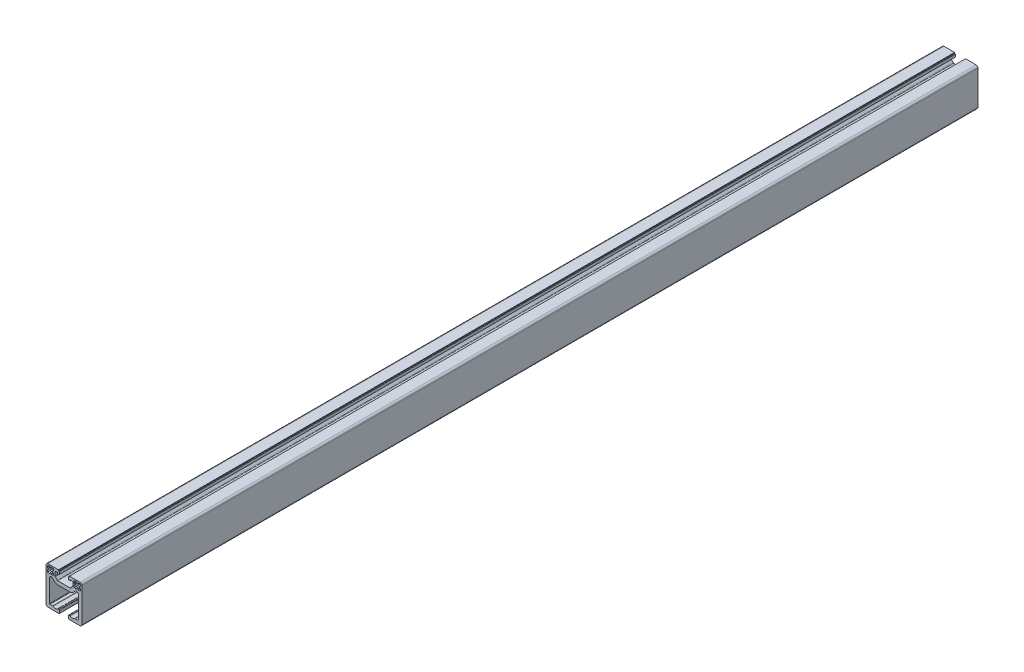
SolidWorks part; units mm, degrees
ref_plane "前视基准面" through (0, 0, 0) normal (0, 0, 1) x (1, 0, 0)
ref_plane "上视基准面" through (0, 0, 0) normal (0, 1, 0) x (1, 0, 0)
ref_plane "右视基准面" through (0, 0, 0) normal (1, 0, 0) x (0, 0, -1)
sketch "Model" plane through (0, 0, 0) normal (0, 0, 1) x (1, 0, 0)
  line L0 (1653.8679, 609.9355) -> (1656.8679, 609.9355)
  line L1 (1662.8679, 609.9355) -> (1663.8679, 609.9355)
  line L2 (1664.3679, 609.4355) -> (1664.3679, 606.4355)
  line L3 (1663.8679, 605.9355) -> (1651.3679, 605.9355)
  line L4 (1649.3679, 607.9355) -> (1649.3679, 645.9355)
  line L5 (1651.3679, 647.9355) -> (1663.2679, 647.9355)
  line L6 (1663.2679, 647.9355) -> (1663.2679, 646.9355)
  line L7 (1663.2679, 646.9355) -> (1664.2679, 646.9355)
  line L8 (1664.2679, 646.9355) -> (1664.2679, 643.9355)
  line L9 (1664.2679, 643.9355) -> (1662.2679, 643.9355)
  line L10 (1662.2679, 643.9355) -> (1662.2679, 644.9355)
  line L11 (1662.2679, 644.9355) -> (1660.3679, 644.9355)
  line L12 (1659.3679, 643.9355) -> (1659.3679, 640.1175)
  line L13 (1659.6608, 639.4104) -> (1661.8428, 637.2284)
  line L14 (1662.5499, 636.9355) -> (1676.186, 636.9355)
  line L15 (1676.8931, 637.2284) -> (1679.0751, 639.4104)
  line L16 (1679.3679, 640.1175) -> (1679.3679, 643.9355)
  line L17 (1678.3679, 644.9355) -> (1676.4679, 644.9355)
  line L18 (1676.4679, 644.9355) -> (1676.4679, 643.9355)
  line L19 (1676.4679, 643.9355) -> (1674.4679, 643.9355)
  line L20 (1674.4679, 643.9355) -> (1674.4679, 646.9355)
  line L21 (1674.4679, 646.9355) -> (1675.4679, 646.9355)
  line L22 (1675.4679, 646.9355) -> (1675.4679, 647.9355)
  line L23 (1675.4679, 647.9355) -> (1687.3679, 647.9355)
  line L24 (1689.3679, 645.9355) -> (1689.3679, 607.9355)
  line L25 (1687.3679, 605.9355) -> (1674.8679, 605.9355)
  line L26 (1674.3679, 606.4355) -> (1674.3679, 609.4355)
  line L27 (1674.8679, 609.9355) -> (1675.8679, 609.9355)
  line L28 (1681.8679, 609.9355) -> (1684.8679, 609.9355)
  line L29 (1685.3679, 610.4355) -> (1685.3679, 635.218)
  line L30 (1681.9537, 636.6322) -> (1679.7215, 634.4)
  line L31 (1676.186, 632.9355) -> (1662.5499, 632.9355)
  line L32 (1659.0144, 634.4) -> (1656.7822, 636.6322)
  line L33 (1653.3679, 635.218) -> (1653.3679, 610.4355)
  line L34 (1657.8679, 639.4355) -> (1655.1679, 639.4355)
  line L35 (1686.8679, 643.7355) -> (1687.8679, 643.7355)
  line L36 (1687.8679, 643.7355) -> (1687.8679, 645.4355)
  line L37 (1686.8679, 642.1355) -> (1686.8679, 643.7355)
  line L38 (1687.8679, 642.1355) -> (1686.8679, 642.1355)
  line L39 (1686.8679, 646.4355) -> (1685.1679, 646.4355)
  line L40 (1687.8679, 639.4355) -> (1687.8679, 642.1355)
  line L41 (1685.1679, 646.4355) -> (1685.1679, 645.4355)
  line L42 (1685.1679, 639.4355) -> (1687.8679, 639.4355)
  line L43 (1685.1679, 645.4355) -> (1683.5679, 645.4355)
  line L44 (1685.1679, 640.4355) -> (1685.1679, 639.4355)
  line L45 (1683.5679, 645.4355) -> (1683.5679, 646.4355)
  line L46 (1683.5679, 640.4355) -> (1685.1679, 640.4355)
  line L47 (1683.5679, 646.4355) -> (1680.8679, 646.4355)
  line L48 (1683.5679, 639.4355) -> (1683.5679, 640.4355)
  line L49 (1680.8679, 646.4355) -> (1680.8679, 643.7355)
  line L50 (1680.8679, 639.4355) -> (1683.5679, 639.4355)
  line L51 (1680.8679, 643.7355) -> (1681.8679, 643.7355)
  line L52 (1680.8679, 642.1355) -> (1680.8679, 639.4355)
  line L53 (1681.8679, 643.7355) -> (1681.8679, 642.1355)
  line L54 (1681.8679, 642.1355) -> (1680.8679, 642.1355)
  line L55 (1656.8679, 643.7355) -> (1657.8679, 643.7355)
  line L56 (1657.8679, 643.7355) -> (1657.8679, 646.4355)
  line L57 (1656.8679, 642.1355) -> (1656.8679, 643.7355)
  line L58 (1657.8679, 646.4355) -> (1655.1679, 646.4355)
  line L59 (1657.8679, 642.1355) -> (1656.8679, 642.1355)
  line L60 (1655.1679, 646.4355) -> (1655.1679, 645.4355)
  line L61 (1657.8679, 639.4355) -> (1657.8679, 642.1355)
  line L62 (1655.1679, 645.4355) -> (1653.5679, 645.4355)
  line L63 (1655.1679, 639.4355) -> (1657.8679, 639.4355)
  line L64 (1653.5679, 645.4355) -> (1653.5679, 646.4355)
  line L65 (1655.1679, 640.4355) -> (1655.1679, 639.4355)
  line L66 (1653.5679, 646.4355) -> (1651.8679, 646.4355)
  line L67 (1653.5679, 640.4355) -> (1655.1679, 640.4355)
  line L68 (1653.5679, 639.4355) -> (1653.5679, 640.4355)
  line L69 (1650.8679, 645.4355) -> (1650.8679, 643.7355)
  line L70 (1650.8679, 639.4355) -> (1653.5679, 639.4355)
  line L71 (1650.8679, 643.7355) -> (1651.8679, 643.7355)
  line L72 (1650.8679, 642.1355) -> (1650.8679, 639.4355)
  line L73 (1651.8679, 643.7355) -> (1651.8679, 642.1355)
  line L74 (1651.8679, 642.1355) -> (1650.8679, 642.1355)
  line L75 (1657.8679, 639.4355) -> (1655.1679, 639.4355)
  line L76 (1655.1679, 639.4355) -> (1655.1679, 640.4355)
  line L77 (1655.1679, 640.4355) -> (1653.5679, 640.4355)
  line L78 (1653.5679, 640.4355) -> (1653.5679, 639.4355)
  line L79 (1653.5679, 639.4355) -> (1650.8679, 639.4355)
  line L80 (1650.8679, 639.4355) -> (1650.8679, 642.1355)
  line L81 (1650.8679, 642.1355) -> (1651.8679, 642.1355)
  line L82 (1651.8679, 642.1355) -> (1651.8679, 643.7355)
  line L83 (1651.8679, 643.7355) -> (1650.8679, 643.7355)
  line L84 (1650.8679, 643.7355) -> (1650.8679, 645.4355)
  line L85 (1651.8679, 646.4355) -> (1653.5679, 646.4355)
  line L86 (1653.5679, 646.4355) -> (1653.5679, 645.4355)
  line L87 (1653.5679, 645.4355) -> (1655.1679, 645.4355)
  line L88 (1655.1679, 645.4355) -> (1655.1679, 646.4355)
  line L89 (1655.1679, 646.4355) -> (1657.8679, 646.4355)
  line L90 (1657.8679, 646.4355) -> (1657.8679, 643.7355)
  line L91 (1657.8679, 643.7355) -> (1656.8679, 643.7355)
  line L92 (1656.8679, 643.7355) -> (1656.8679, 642.1355)
  line L93 (1656.8679, 642.1355) -> (1657.8679, 642.1355)
  line L94 (1657.8679, 642.1355) -> (1657.8679, 639.4355)
  line L95 (1680.8679, 639.4355) -> (1680.8679, 642.1355)
  line L96 (1680.8679, 642.1355) -> (1681.8679, 642.1355)
  line L97 (1681.8679, 642.1355) -> (1681.8679, 643.7355)
  line L98 (1681.8679, 643.7355) -> (1680.8679, 643.7355)
  line L99 (1680.8679, 643.7355) -> (1680.8679, 646.4355)
  line L100 (1680.8679, 646.4355) -> (1683.5679, 646.4355)
  line L101 (1683.5679, 646.4355) -> (1683.5679, 645.4355)
  line L102 (1683.5679, 645.4355) -> (1685.1679, 645.4355)
  line L103 (1685.1679, 645.4355) -> (1685.1679, 646.4355)
  line L104 (1685.1679, 646.4355) -> (1686.8679, 646.4355)
  line L105 (1687.8679, 645.4355) -> (1687.8679, 643.7355)
  line L106 (1687.8679, 643.7355) -> (1686.8679, 643.7355)
  line L107 (1686.8679, 643.7355) -> (1686.8679, 642.1355)
  line L108 (1686.8679, 642.1355) -> (1687.8679, 642.1355)
  line L109 (1687.8679, 642.1355) -> (1687.8679, 639.4355)
  line L110 (1687.8679, 639.4355) -> (1685.1679, 639.4355)
  line L111 (1685.1679, 639.4355) -> (1685.1679, 640.4355)
  line L112 (1685.1679, 640.4355) -> (1683.5679, 640.4355)
  line L113 (1683.5679, 640.4355) -> (1683.5679, 639.4355)
  line L114 (1683.5679, 639.4355) -> (1680.8679, 639.4355)
  line L115 (1687.3679, 647.9355) -> (1675.4679, 647.9355)
  line L116 (1675.4679, 647.9355) -> (1675.4679, 646.9355)
  line L117 (1675.4679, 646.9355) -> (1674.4679, 646.9355)
  line L118 (1674.4679, 646.9355) -> (1674.4679, 643.9355)
  line L119 (1674.4679, 643.9355) -> (1676.4679, 643.9355)
  line L120 (1676.4679, 643.9355) -> (1676.4679, 644.9355)
  line L121 (1676.4679, 644.9355) -> (1678.3679, 644.9355)
  line L122 (1679.3679, 643.9355) -> (1679.3679, 640.1175)
  line L123 (1679.0751, 639.4104) -> (1676.8931, 637.2284)
  line L124 (1676.186, 636.9355) -> (1662.5499, 636.9355)
  line L125 (1661.8428, 637.2284) -> (1659.6608, 639.4104)
  line L126 (1659.3679, 640.1175) -> (1659.3679, 643.9355)
  line L127 (1660.3679, 644.9355) -> (1662.2679, 644.9355)
  line L128 (1662.2679, 644.9355) -> (1662.2679, 643.9355)
  line L129 (1662.2679, 643.9355) -> (1664.2679, 643.9355)
  line L130 (1664.2679, 643.9355) -> (1664.2679, 646.9355)
  line L131 (1664.2679, 646.9355) -> (1663.2679, 646.9355)
  line L132 (1663.2679, 646.9355) -> (1663.2679, 647.9355)
  line L133 (1663.2679, 647.9355) -> (1651.3679, 647.9355)
  line L134 (1649.3679, 645.9355) -> (1649.3679, 607.9355)
  line L135 (1651.3679, 605.9355) -> (1663.8679, 605.9355)
  line L136 (1664.3679, 606.4355) -> (1664.3679, 609.4355)
  line L137 (1663.8679, 609.9355) -> (1662.8679, 609.9355)
  line L138 (1656.8679, 609.9355) -> (1653.8679, 609.9355)
  line L139 (1653.3679, 610.4355) -> (1653.3679, 635.218)
  line L140 (1656.7822, 636.6322) -> (1659.0144, 634.4)
  line L141 (1662.5499, 632.9355) -> (1676.186, 632.9355)
  line L142 (1679.7215, 634.4) -> (1681.9537, 636.6322)
  line L143 (1685.3679, 635.218) -> (1685.3679, 610.4355)
  line L144 (1684.8679, 609.9355) -> (1681.8679, 609.9355)
  line L145 (1675.8679, 609.9355) -> (1674.8679, 609.9355)
  line L146 (1674.3679, 609.4355) -> (1674.3679, 606.4355)
  line L147 (1674.8679, 605.9355) -> (1687.3679, 605.9355)
  line L148 (1689.3679, 607.9355) -> (1689.3679, 645.9355)
  line L149 (1655.1679, 639.4355) -> (1655.1679, 640.4355)
  line L150 (1655.1679, 640.4355) -> (1653.5679, 640.4355)
  line L151 (1653.5679, 640.4355) -> (1653.5679, 639.4355)
  line L152 (1653.5679, 639.4355) -> (1650.8679, 639.4355)
  line L153 (1650.8679, 639.4355) -> (1650.8679, 642.1355)
  line L154 (1650.8679, 642.1355) -> (1651.8679, 642.1355)
  line L155 (1651.8679, 642.1355) -> (1651.8679, 643.7355)
  line L156 (1651.8679, 643.7355) -> (1650.8679, 643.7355)
  line L157 (1650.8679, 643.7355) -> (1650.8679, 645.4355)
  line L158 (1651.8679, 646.4355) -> (1653.5679, 646.4355)
  line L159 (1653.5679, 646.4355) -> (1653.5679, 645.4355)
  line L160 (1653.5679, 645.4355) -> (1655.1679, 645.4355)
  line L161 (1655.1679, 645.4355) -> (1655.1679, 646.4355)
  line L162 (1655.1679, 646.4355) -> (1657.8679, 646.4355)
  line L163 (1657.8679, 646.4355) -> (1657.8679, 643.7355)
  line L164 (1657.8679, 643.7355) -> (1656.8679, 643.7355)
  line L165 (1656.8679, 643.7355) -> (1656.8679, 642.1355)
  line L166 (1656.8679, 642.1355) -> (1657.8679, 642.1355)
  line L167 (1657.8679, 642.1355) -> (1657.8679, 639.4355)
  line L168 (1657.8679, 639.4355) -> (1655.1679, 639.4355)
  line L169 (1680.8679, 642.1355) -> (1681.8679, 642.1355)
  line L170 (1681.8679, 642.1355) -> (1681.8679, 643.7355)
  line L171 (1681.8679, 643.7355) -> (1680.8679, 643.7355)
  line L172 (1680.8679, 643.7355) -> (1680.8679, 646.4355)
  line L173 (1680.8679, 646.4355) -> (1683.5679, 646.4355)
  line L174 (1683.5679, 646.4355) -> (1683.5679, 645.4355)
  line L175 (1683.5679, 645.4355) -> (1685.1679, 645.4355)
  line L176 (1685.1679, 645.4355) -> (1685.1679, 646.4355)
  line L177 (1685.1679, 646.4355) -> (1686.8679, 646.4355)
  line L178 (1687.8679, 645.4355) -> (1687.8679, 643.7355)
  line L179 (1687.8679, 643.7355) -> (1686.8679, 643.7355)
  line L180 (1686.8679, 643.7355) -> (1686.8679, 642.1355)
  line L181 (1686.8679, 642.1355) -> (1687.8679, 642.1355)
  line L182 (1687.8679, 642.1355) -> (1687.8679, 639.4355)
  line L183 (1687.8679, 639.4355) -> (1685.1679, 639.4355)
  line L184 (1685.1679, 639.4355) -> (1685.1679, 640.4355)
  line L185 (1685.1679, 640.4355) -> (1683.5679, 640.4355)
  line L186 (1683.5679, 640.4355) -> (1683.5679, 639.4355)
  line L187 (1683.5679, 639.4355) -> (1680.8679, 639.4355)
  line L188 (1680.8679, 639.4355) -> (1680.8679, 642.1355)
  line L189 (1679.7215, 634.4) -> (1681.9537, 636.6322)
  line L190 (1685.3679, 635.218) -> (1685.3679, 610.4355)
  line L191 (1684.8679, 609.9355) -> (1681.8679, 609.9355)
  line L192 (1675.8679, 609.9355) -> (1674.8679, 609.9355)
  line L193 (1674.3679, 609.4355) -> (1674.3679, 606.4355)
  line L194 (1674.8679, 605.9355) -> (1687.3679, 605.9355)
  line L195 (1689.3679, 607.9355) -> (1689.3679, 645.9355)
  line L196 (1687.3679, 647.9355) -> (1675.4679, 647.9355)
  line L197 (1675.4679, 647.9355) -> (1675.4679, 646.9355)
  line L198 (1675.4679, 646.9355) -> (1674.4679, 646.9355)
  line L199 (1674.4679, 646.9355) -> (1674.4679, 643.9355)
  line L200 (1674.4679, 643.9355) -> (1676.4679, 643.9355)
  line L201 (1676.4679, 643.9355) -> (1676.4679, 644.9355)
  line L202 (1676.4679, 644.9355) -> (1678.3679, 644.9355)
  line L203 (1679.3679, 643.9355) -> (1679.3679, 640.1175)
  line L204 (1679.0751, 639.4104) -> (1676.8931, 637.2284)
  line L205 (1676.186, 636.9355) -> (1662.5499, 636.9355)
  line L206 (1661.8428, 637.2284) -> (1659.6608, 639.4104)
  line L207 (1659.3679, 640.1175) -> (1659.3679, 643.9355)
  line L208 (1660.3679, 644.9355) -> (1662.2679, 644.9355)
  line L209 (1662.2679, 644.9355) -> (1662.2679, 643.9355)
  line L210 (1662.2679, 643.9355) -> (1664.2679, 643.9355)
  line L211 (1664.2679, 643.9355) -> (1664.2679, 646.9355)
  line L212 (1664.2679, 646.9355) -> (1663.2679, 646.9355)
  line L213 (1663.2679, 646.9355) -> (1663.2679, 647.9355)
  line L214 (1663.2679, 647.9355) -> (1651.3679, 647.9355)
  line L215 (1649.3679, 645.9355) -> (1649.3679, 607.9355)
  line L216 (1651.3679, 605.9355) -> (1663.8679, 605.9355)
  line L217 (1664.3679, 606.4355) -> (1664.3679, 609.4355)
  line L218 (1663.8679, 609.9355) -> (1662.8679, 609.9355)
  line L219 (1656.8679, 609.9355) -> (1653.8679, 609.9355)
  line L220 (1653.3679, 610.4355) -> (1653.3679, 635.218)
  line L221 (1656.7822, 636.6322) -> (1659.0144, 634.4)
  line L222 (1662.5499, 632.9355) -> (1676.186, 632.9355)
  arc A0 (1657.1679, 609.8355) -> (1656.8679, 609.9355) centre (1656.8679, 609.4355) ccw
  arc A1 (1657.1679, 609.8355) -> (1662.5679, 609.8355) centre (1659.8679, 613.4355) ccw
  arc A2 (1662.8679, 609.9355) -> (1662.5679, 609.8355) centre (1662.8679, 609.4355) ccw
  arc A3 (1664.3679, 609.4355) -> (1663.8679, 609.9355) centre (1663.8679, 609.4355) ccw
  arc A4 (1663.8679, 605.9355) -> (1664.3679, 606.4355) centre (1663.8679, 606.4355) ccw
  arc A5 (1649.3679, 607.9355) -> (1651.3679, 605.9355) centre (1651.3679, 607.9355) ccw
  arc A6 (1651.3679, 647.9355) -> (1649.3679, 645.9355) centre (1651.3679, 645.9355) ccw
  arc A7 (1660.3679, 644.9355) -> (1659.3679, 643.9355) centre (1660.3679, 643.9355) ccw
  arc A8 (1659.3679, 640.1175) -> (1659.6608, 639.4104) centre (1660.3679, 640.1175) ccw
  arc A9 (1661.8428, 637.2284) -> (1662.5499, 636.9355) centre (1662.5499, 637.9355) ccw
  arc A10 (1676.186, 636.9355) -> (1676.8931, 637.2284) centre (1676.186, 637.9355) ccw
  arc A11 (1679.0751, 639.4104) -> (1679.3679, 640.1175) centre (1678.3679, 640.1175) ccw
  arc A12 (1679.3679, 643.9355) -> (1678.3679, 644.9355) centre (1678.3679, 643.9355) ccw
  arc A13 (1689.3679, 645.9355) -> (1687.3679, 647.9355) centre (1687.3679, 645.9355) ccw
  arc A14 (1687.3679, 605.9355) -> (1689.3679, 607.9355) centre (1687.3679, 607.9355) ccw
  arc A15 (1674.3679, 606.4355) -> (1674.8679, 605.9355) centre (1674.8679, 606.4355) ccw
  arc A16 (1674.8679, 609.9355) -> (1674.3679, 609.4355) centre (1674.8679, 609.4355) ccw
  arc A17 (1676.1679, 609.8355) -> (1675.8679, 609.9355) centre (1675.8679, 609.4355) ccw
  arc A18 (1676.1679, 609.8355) -> (1681.5679, 609.8355) centre (1678.8679, 613.4355) ccw
  arc A19 (1681.8679, 609.9355) -> (1681.5679, 609.8355) centre (1681.8679, 609.4355) ccw
  arc A20 (1684.8679, 609.9355) -> (1685.3679, 610.4355) centre (1684.8679, 610.4355) ccw
  arc A21 (1685.3679, 635.218) -> (1681.9537, 636.6322) centre (1683.3679, 635.218) ccw
  arc A22 (1676.186, 632.9355) -> (1679.7215, 634.4) centre (1676.186, 637.9355) ccw
  arc A23 (1659.0144, 634.4) -> (1662.5499, 632.9355) centre (1662.5499, 637.9355) ccw
  arc A24 (1656.7822, 636.6322) -> (1653.3679, 635.218) centre (1655.3679, 635.218) ccw
  arc A25 (1653.3679, 610.4355) -> (1653.8679, 609.9355) centre (1653.8679, 610.4355) ccw
  arc A26 (1687.8679, 645.4355) -> (1686.8679, 646.4355) centre (1686.8679, 645.4355) ccw
  arc A27 (1651.8679, 646.4355) -> (1650.8679, 645.4355) centre (1651.8679, 645.4355) ccw
  arc A28 (1651.8679, 646.4355) -> (1650.8679, 645.4355) centre (1651.8679, 645.4355) ccw
  arc A29 (1687.8679, 645.4355) -> (1686.8679, 646.4355) centre (1686.8679, 645.4355) ccw
  arc A30 (1689.3679, 645.9355) -> (1687.3679, 647.9355) centre (1687.3679, 645.9355) ccw
  arc A31 (1679.3679, 643.9355) -> (1678.3679, 644.9355) centre (1678.3679, 643.9355) ccw
  arc A32 (1679.0751, 639.4104) -> (1679.3679, 640.1175) centre (1678.3679, 640.1175) ccw
  arc A33 (1676.186, 636.9355) -> (1676.8931, 637.2284) centre (1676.186, 637.9355) ccw
  arc A34 (1661.8428, 637.2284) -> (1662.5499, 636.9355) centre (1662.5499, 637.9355) ccw
  arc A35 (1659.3679, 640.1175) -> (1659.6608, 639.4104) centre (1660.3679, 640.1175) ccw
  arc A36 (1660.3679, 644.9355) -> (1659.3679, 643.9355) centre (1660.3679, 643.9355) ccw
  arc A37 (1651.3679, 647.9355) -> (1649.3679, 645.9355) centre (1651.3679, 645.9355) ccw
  arc A38 (1649.3679, 607.9355) -> (1651.3679, 605.9355) centre (1651.3679, 607.9355) ccw
  arc A39 (1663.8679, 605.9355) -> (1664.3679, 606.4355) centre (1663.8679, 606.4355) ccw
  arc A40 (1664.3679, 609.4355) -> (1663.8679, 609.9355) centre (1663.8679, 609.4355) ccw
  arc A41 (1662.8679, 609.9355) -> (1662.5679, 609.8355) centre (1662.8679, 609.4355) ccw
  arc A42 (1657.1679, 609.8355) -> (1662.5679, 609.8355) centre (1659.8679, 613.4355) ccw
  arc A43 (1657.1679, 609.8355) -> (1656.8679, 609.9355) centre (1656.8679, 609.4355) ccw
  arc A44 (1653.3679, 610.4355) -> (1653.8679, 609.9355) centre (1653.8679, 610.4355) ccw
  arc A45 (1656.7822, 636.6322) -> (1653.3679, 635.218) centre (1655.3679, 635.218) ccw
  arc A46 (1659.0144, 634.4) -> (1662.5499, 632.9355) centre (1662.5499, 637.9355) ccw
  arc A47 (1676.186, 632.9355) -> (1679.7215, 634.4) centre (1676.186, 637.9355) ccw
  arc A48 (1685.3679, 635.218) -> (1681.9537, 636.6322) centre (1683.3679, 635.218) ccw
  arc A49 (1684.8679, 609.9355) -> (1685.3679, 610.4355) centre (1684.8679, 610.4355) ccw
  arc A50 (1681.8679, 609.9355) -> (1681.5679, 609.8355) centre (1681.8679, 609.4355) ccw
  arc A51 (1676.1679, 609.8355) -> (1681.5679, 609.8355) centre (1678.8679, 613.4355) ccw
  arc A52 (1676.1679, 609.8355) -> (1675.8679, 609.9355) centre (1675.8679, 609.4355) ccw
  arc A53 (1674.8679, 609.9355) -> (1674.3679, 609.4355) centre (1674.8679, 609.4355) ccw
  arc A54 (1674.3679, 606.4355) -> (1674.8679, 605.9355) centre (1674.8679, 606.4355) ccw
  arc A55 (1687.3679, 605.9355) -> (1689.3679, 607.9355) centre (1687.3679, 607.9355) ccw
  arc A56 (1651.8679, 646.4355) -> (1650.8679, 645.4355) centre (1651.8679, 645.4355) ccw
  arc A57 (1687.8679, 645.4355) -> (1686.8679, 646.4355) centre (1686.8679, 645.4355) ccw
  arc A58 (1685.3679, 635.218) -> (1681.9537, 636.6322) centre (1683.3679, 635.218) ccw
  arc A59 (1684.8679, 609.9355) -> (1685.3679, 610.4355) centre (1684.8679, 610.4355) ccw
  arc A60 (1681.8679, 609.9355) -> (1681.5679, 609.8355) centre (1681.8679, 609.4355) ccw
  arc A61 (1676.1679, 609.8355) -> (1681.5679, 609.8355) centre (1678.8679, 613.4355) ccw
  arc A62 (1676.1679, 609.8355) -> (1675.8679, 609.9355) centre (1675.8679, 609.4355) ccw
  arc A63 (1674.8679, 609.9355) -> (1674.3679, 609.4355) centre (1674.8679, 609.4355) ccw
  arc A64 (1674.3679, 606.4355) -> (1674.8679, 605.9355) centre (1674.8679, 606.4355) ccw
  arc A65 (1687.3679, 605.9355) -> (1689.3679, 607.9355) centre (1687.3679, 607.9355) ccw
  arc A66 (1689.3679, 645.9355) -> (1687.3679, 647.9355) centre (1687.3679, 645.9355) ccw
  arc A67 (1679.3679, 643.9355) -> (1678.3679, 644.9355) centre (1678.3679, 643.9355) ccw
  arc A68 (1679.0751, 639.4104) -> (1679.3679, 640.1175) centre (1678.3679, 640.1175) ccw
  arc A69 (1676.186, 636.9355) -> (1676.8931, 637.2284) centre (1676.186, 637.9355) ccw
  arc A70 (1661.8428, 637.2284) -> (1662.5499, 636.9355) centre (1662.5499, 637.9355) ccw
  arc A71 (1659.3679, 640.1175) -> (1659.6608, 639.4104) centre (1660.3679, 640.1175) ccw
  arc A72 (1660.3679, 644.9355) -> (1659.3679, 643.9355) centre (1660.3679, 643.9355) ccw
  arc A73 (1651.3679, 647.9355) -> (1649.3679, 645.9355) centre (1651.3679, 645.9355) ccw
  arc A74 (1649.3679, 607.9355) -> (1651.3679, 605.9355) centre (1651.3679, 607.9355) ccw
  arc A75 (1663.8679, 605.9355) -> (1664.3679, 606.4355) centre (1663.8679, 606.4355) ccw
  arc A76 (1664.3679, 609.4355) -> (1663.8679, 609.9355) centre (1663.8679, 609.4355) ccw
  arc A77 (1662.8679, 609.9355) -> (1662.5679, 609.8355) centre (1662.8679, 609.4355) ccw
  arc A78 (1657.1679, 609.8355) -> (1662.5679, 609.8355) centre (1659.8679, 613.4355) ccw
  arc A79 (1657.1679, 609.8355) -> (1656.8679, 609.9355) centre (1656.8679, 609.4355) ccw
  arc A80 (1653.3679, 610.4355) -> (1653.8679, 609.9355) centre (1653.8679, 610.4355) ccw
  arc A81 (1656.7822, 636.6322) -> (1653.3679, 635.218) centre (1655.3679, 635.218) ccw
  arc A82 (1659.0144, 634.4) -> (1662.5499, 632.9355) centre (1662.5499, 637.9355) ccw
  arc A83 (1676.186, 632.9355) -> (1679.7215, 634.4) centre (1676.186, 637.9355) ccw
extrude "凸台-拉伸1" add sketch "Model" along normal blind 1000 contours A25 L33 A24 L32 A23 L31 A22 L30 A21 L29 A20 L28 A19 A18 A17 L27 A16 L26 A15 L25 A14 L24 A13 L23 L22 L21 L20 L19 L18 L17 A12 L16 A11 L15 A10 L14 A9 L13 A8 L12 A7 L11 L10 L9 L8 L7 L6 L5 A6 L4 A5
